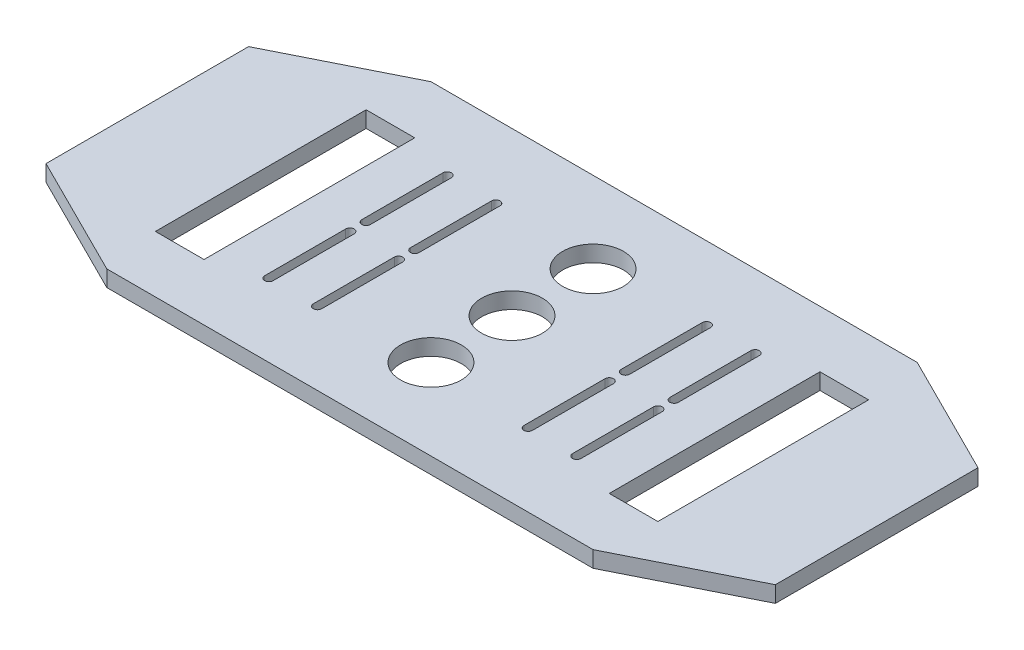
SolidWorks part; units mm, degrees
material "Pin"
ref_plane "Plan de face" through (0, 0, 0) normal (0, 0, 1) x (1, 0, 0)
ref_plane "Plan de dessus" through (0, 0, 0) normal (0, 1, 0) x (1, 0, 0)
ref_plane "Plan de droite" through (0, 0, 0) normal (1, 0, 0) x (0, 0, -1)
sketch "Esquisse1" plane through (0, 0, 0) normal (0, 1, 0) x (1, 0, 0)
  line L1 (0, 0) -> (180, 0)
  line L2 (0, 0) -> (0, 80)
  line L3 (0, 80) -> (180, 80)
  line L4 (180, 0) -> (180, 80)
  dimension "D1" = 80
  dimension "D2" = 180
extrude "Boss.-Extru.1" add sketch "Esquisse1" along normal blind 4
sketch "Esquisse2" plane through (0, 4, 0) normal (0, 1, 0) x (1, 0, 0)
  line L0 (0, 65) -> (30, 80)
  line L1 (0, 80) -> (0, 0) construction
  line L2 (180, 80) -> (0, 80) construction
  line L3 (150, 80) -> (180, 65)
  line L4 (180, 0) -> (180, 80) construction
  line L5 (150, 0) -> (180, 15)
  line L6 (0, 0) -> (180, 0) construction
  line L7 (0, 15) -> (30, 0)
  line L8 (0, 80) -> (30, 80)
  line L9 (0, 15) -> (0, 0)
  line L10 (0, 0) -> (30, 0)
  line L11 (150, 0) -> (180, 0)
  line L12 (180, 0) -> (180, 15)
  line L13 (180, 65) -> (180, 80)
  line L14 (180, 80) -> (150, 80)
  line L15 (0, 80) -> (0, 65)
  dimension "D1" = 15
  dimension "D2" = 30
  dimension "D3" = 15
  dimension "D4" = 30
  dimension "D5" = 30
  dimension "D6" = 15
  dimension "D7" = 15
  dimension "D8" = 30
extrude "Enlèv. mat.-Extru.2" cut sketch "Esquisse2" against normal blind 4
sketch "Esquisse7" plane through (0, 4, 0) normal (0, 1, 0) x (1, 0, 0)
  line L0 (64, 18) -> (64, 38) construction
  line L1 (62.95, 18) -> (62.95, 38)
  line L2 (65.05, 18) -> (65.05, 38)
  line L3 (52, 18) -> (52, 38) construction
  line L4 (50.95, 18) -> (50.95, 38)
  line L5 (53.05, 18) -> (53.05, 38)
  line L6 (3.5692, 40) -> (183.2325, 40) construction
  line L7 (52, 42) -> (52, 62) construction
  line L8 (50.95, 42) -> (50.95, 62)
  line L9 (53.05, 42) -> (53.05, 62)
  line L10 (64, 42) -> (64, 62) construction
  line L11 (62.95, 42) -> (62.95, 62)
  line L12 (65.05, 42) -> (65.05, 62)
  line L13 (30, 0) -> (150, 0) construction
  line L14 (90, -22.0489) -> (90, 126.4706) construction
  line L15 (0, 65) -> (0, 15) construction
  line L16 (116, 42) -> (116, 62) construction
  line L17 (117.05, 42) -> (117.05, 62)
  line L18 (114.95, 42) -> (114.95, 62)
  line L19 (128, 42) -> (128, 62) construction
  line L20 (129.05, 42) -> (129.05, 62)
  line L21 (126.95, 42) -> (126.95, 62)
  line L22 (128, 18) -> (128, 38) construction
  line L23 (129.05, 18) -> (129.05, 38)
  line L24 (126.95, 18) -> (126.95, 38)
  line L25 (116, 18) -> (116, 38) construction
  line L26 (117.05, 18) -> (117.05, 38)
  line L27 (114.95, 18) -> (114.95, 38)
  arc A0 (62.95, 18) -> (65.05, 18) centre (64, 18) ccw
  arc A1 (65.05, 38) -> (62.95, 38) centre (64, 38) ccw
  arc A2 (50.95, 18) -> (53.05, 18) centre (52, 18) ccw
  arc A3 (53.05, 38) -> (50.95, 38) centre (52, 38) ccw
  arc A4 (50.95, 42) -> (53.05, 42) centre (52, 42) ccw
  arc A5 (53.05, 62) -> (50.95, 62) centre (52, 62) ccw
  arc A6 (62.95, 42) -> (65.05, 42) centre (64, 42) ccw
  arc A7 (65.05, 62) -> (62.95, 62) centre (64, 62) ccw
  arc A8 (117.05, 42) -> (114.95, 42) centre (116, 42) cw
  arc A9 (114.95, 62) -> (117.05, 62) centre (116, 62) cw
  arc A10 (129.05, 42) -> (126.95, 42) centre (128, 42) cw
  arc A11 (126.95, 62) -> (129.05, 62) centre (128, 62) cw
  arc A12 (129.05, 18) -> (126.95, 18) centre (128, 18) cw
  arc A13 (126.95, 38) -> (129.05, 38) centre (128, 38) cw
  arc A14 (117.05, 18) -> (114.95, 18) centre (116, 18) cw
  arc A15 (114.95, 38) -> (117.05, 38) centre (116, 38) cw
  point P2 (64, 28)
  point P7 (52, 28)
  point P18 (52, 52)
  point P23 (64, 52)
  point P38 (116, 52)
  point P45 (128, 52)
  point P52 (128, 28)
  point P59 (116, 28)
  dimension "D1" = 12
  dimension "D2" = 24
  dimension "D3" = 2.1
  dimension "D4" = 2.1
  dimension "D5" = 2.1
  dimension "D6" = 2.1
  dimension "D7" = 12
  dimension "D8" = 24
  dimension "D9" = 20
  dimension "D10" = 20
  dimension "D11" = 20
  dimension "D12" = 20
  dimension "D13" = 12
  dimension "D14" = 12
  dimension "D15" = 40
  dimension "D16" = 90
  dimension "D17" = 26
extrude "Enlèv. mat.-Extru.3" cut sketch "Esquisse7" against normal blind 4
sketch "Esquisse8" plane through (0, 4, 0) normal (0, 1, 0) x (1, 0, 0)
  line L0 (30, 0) -> (150, 0) construction
  line L1 (152, 14) -> (140, 14)
  line L2 (152, 14) -> (152, 66)
  line L3 (152, 66) -> (140, 66)
  line L4 (140, 14) -> (140, 66)
  line L5 (150, 80) -> (30, 80) construction
  line L6 (180, 15) -> (180, 65) construction
  line L7 (90, -18.8233) -> (90, 100.9903) construction
  line L8 (28, 66) -> (40, 66)
  line L9 (40, 14) -> (40, 66)
  line L10 (28, 14) -> (40, 14)
  line L11 (28, 14) -> (28, 66)
  dimension "D1" = 14
  dimension "D2" = 14
  dimension "D3" = 12
  dimension "D4" = 28
  dimension "D5" = 90
extrude "Enlèv. mat.-Extru.4" cut sketch "Esquisse8" against normal up to next
sketch "Esquisse9" plane through (0, 0, 0) normal (0, -1, 0) x (1, 0, 0)
  line L1 (150, -80) -> (30, -80) construction
  line L2 (0, -65) -> (0, -15) construction
  circle A0 centre (90, -60) radius 7.5
  circle A1 centre (90, -40) radius 7.5
  circle A2 centre (90, -20) radius 7.5
  point P8 (0, 0)
  point P9 (85.0264, -59.3581)
  point P10 (0, -28.0243)
  dimension "D1" = 15
  dimension "D2" = 15
  dimension "D3" = 15
  dimension "D4" = 20
  dimension "D5" = 40
  dimension "D6" = 90
  dimension "D7" = 20
extrude "Enlèv. mat.-Extru.5" cut sketch "Esquisse9" against normal up to next
equation "\"D3@Esquisse2\"=\"D1@Esquisse2\""
equation "\"D7@Esquisse2\"=\"D1@Esquisse2\""
equation "\"D6@Esquisse2\"=15"
